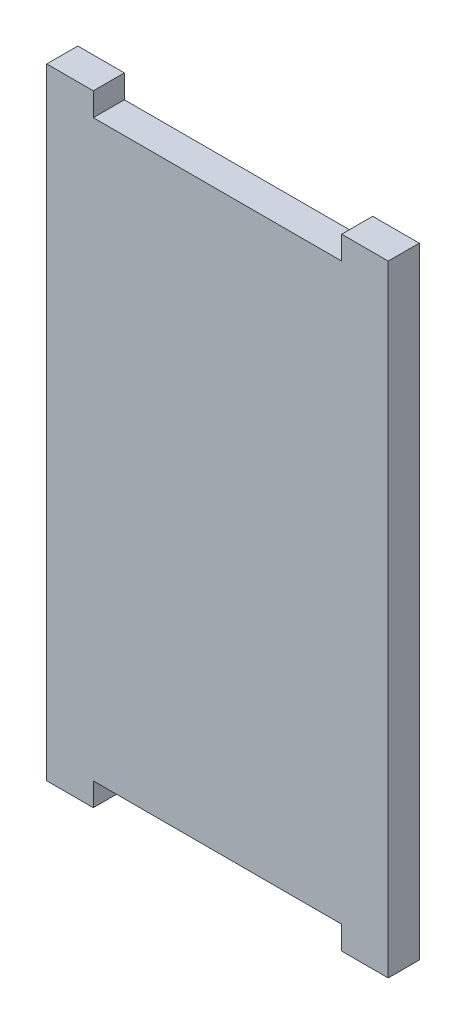
SolidWorks part; units mm, degrees
ref_plane "정면" through (0, 0, 0) normal (0, 0, 1) x (1, 0, 0)
ref_plane "윗면" through (0, 0, 0) normal (0, 1, 0) x (1, 0, 0)
ref_plane "우측면" through (0, 0, 0) normal (1, 0, 0) x (0, 0, -1)
sketch "스케치4" plane through (0, 0, 0) normal (0, 0, 1) x (1, 0, 0)
  line L1 (0, 0) -> (44, 0)
  line L2 (0, 0) -> (0, 80)
  line L3 (0, 80) -> (44, 80)
  line L4 (44, 0) -> (44, 80)
  dimension "D1" = 80
  dimension "D2" = 44
extrude "보스-돌출2" add sketch "스케치4" along normal blind 4
sketch "스케치6" plane through (0, 0, 4) normal (0, 0, 1) x (1, 0, 0)
  line L0 (0, 0) -> (44, 0) construction
  line L1 (-6.3351, 40) -> (51.5653, 40) construction
  line L2 (44, 80) -> (0, 80) construction
  line L3 (38, 77) -> (38, 80)
  line L4 (6, 0) -> (6, 3)
  line L5 (6, 3) -> (38, 3)
  line L6 (38, 3) -> (38, 0)
  line L7 (6, 80) -> (38, 80)
  line L8 (6, 0) -> (38, 0)
  line L9 (6, 80) -> (6, 77)
  line L10 (6, 77) -> (38, 77)
  point P0 (3, 0)
  point P1 (22, 0)
  point P4 (41, 0)
  point P7 (41, 80)
  point P8 (3, 80)
  point P9 (28, 0)
  point P10 (16, 80)
  point P11 (22, 80)
  dimension "D1" = 19
  dimension "D2" = 19
  dimension "D3" = 6
  dimension "D4" = 6
  dimension "D5" = 3
  dimension "D6" = 3
extrude "컷-돌출1" cut sketch "스케치6" against normal through all
